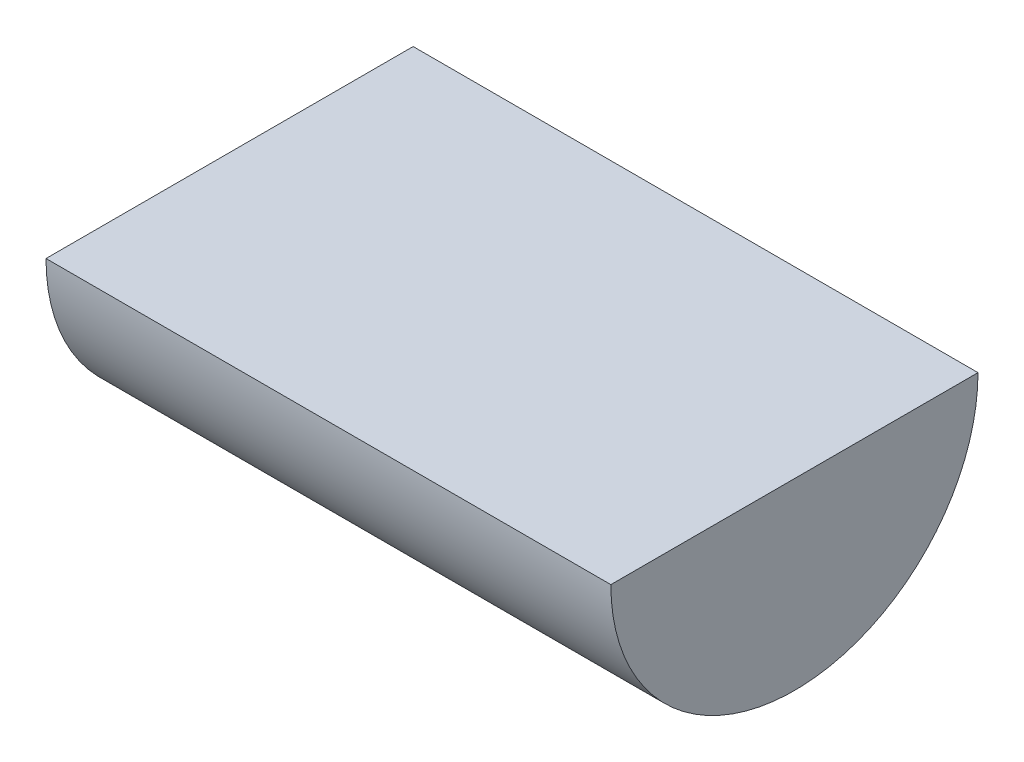
SolidWorks part; units mm, degrees
ref_plane "Front Plane" through (0, 0, 0) normal (0, 0, 1) x (1, 0, 0)
ref_plane "Top Plane" through (0, 0, 0) normal (0, 1, 0) x (1, 0, 0)
ref_plane "Right Plane" through (0, 0, 0) normal (1, 0, 0) x (0, 0, -1)
sketch "Sketch1" plane through (0, 0, 0) normal (1, 0, 0) x (0, 0, -1)
  circle A0 centre (0, 0) radius 19.5
  dimension "D1" = 39
extrude "Boss-Extrude1" add sketch "Sketch1" along normal blind 60
sketch "Sketch2" plane through (0, 0, 0) normal (1, 0, 0) x (0, 0, -1)
  line L0 (21.45, 0) -> (-21.45, 0) construction
  line L1 (21.5496, 0) -> (-23.9585, 0)
  line L2 (21.5496, 0) -> (21.5496, 21.0451)
  line L3 (21.5496, 21.0451) -> (-23.9585, 21.0451)
  line L4 (-23.9585, 0) -> (-23.9585, 21.0451)
extrude "Cut-Extrude1" cut sketch "Sketch2" along normal blind 75
